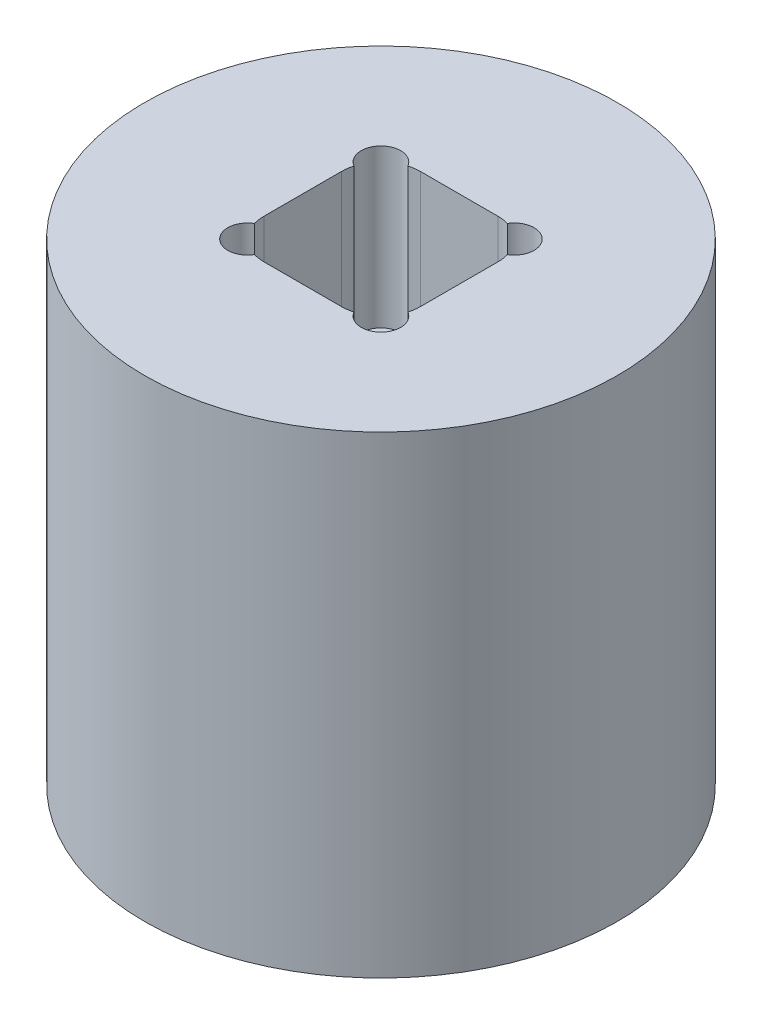
SolidWorks part; units mm, degrees
ref_plane "Front Plane" through (0, 0, 0) normal (0, 0, 1) x (1, 0, 0)
ref_plane "Top Plane" through (0, 0, 0) normal (0, 1, 0) x (1, 0, 0)
ref_plane "Right Plane" through (0, 0, 0) normal (1, 0, 0) x (0, 0, -1)
sketch "Sketch1" plane through (0, 0, 0) normal (0, 1, 0) x (1, 0, 0)
  circle A0 centre (0, 0) radius 19.05
  dimension "D1" = 38.1
extrude "Boss-Extrude1" add sketch "Sketch1" along normal mid plane 38.1
sketch "Sketch2" plane through (0, 19.05, 0) normal (0, 1, 0) x (1, 0, 0)
  line L1 (6.3056, -6.3056) -> (-6.3056, -6.3056)
  line L2 (6.3056, -6.3056) -> (6.3056, 6.3056)
  line L3 (6.3056, 6.3056) -> (-6.3056, 6.3055)
  line L4 (-6.3056, -6.3056) -> (-6.3056, 6.3055)
  line L5 (6.3056, -6.3056) -> (-6.3056, 6.3055) construction
  line L6 (6.3056, 6.3056) -> (-6.3056, -6.3056) construction
  circle A0 centre (-6.3056, 6.3055) radius 1.5875
  circle A1 centre (-6.3056, -6.3056) radius 1.5875
  circle A2 centre (6.3056, -6.3056) radius 1.5875
  circle A3 centre (6.3056, 6.3056) radius 1.5875
  point P0 (0, 0)
  dimension "D2" = 3.175
  dimension "D1" = 12.6111
extrude "Cut-Extrude1" cut sketch "Sketch2" against normal blind 12.7 contours L4 A0 L3 | A3 L3 A0 L4 A1 L1 A2 L2 | L1 A1 L4 | L2 A2 L1 | L3 A3 L2
sketch "Sketch3" plane through (0, -19.05, 0) normal (0, -1, 0) x (1, 0, 0)
  line L1 (9.1249, 12.3) -> (-9.125, 12.3)
  line L2 (12.2999, 9.125) -> (12.2999, -9.1249)
  line L3 (9.1249, -12.3) -> (-9.125, -12.3)
  line L4 (-12.3, 9.125) -> (-12.3, -9.125)
  line L5 (12.2999, 12.3) -> (-12.3, -12.3) construction
  line L6 (12.2999, -12.3) -> (-12.3, 12.2999) construction
  arc A0 (9.1249, 12.3) -> (12.2999, 9.125) centre (9.1249, 9.125) cw
  arc A1 (-9.125, 12.3) -> (-12.3, 9.125) centre (-9.125, 9.125) ccw
  arc A2 (-9.125, -12.3) -> (-12.3, -9.125) centre (-9.125, -9.125) cw
  arc A3 (12.2999, -9.1249) -> (9.1249, -12.3) centre (9.1249, -9.125) cw
  point P0 (0, 0)
  dimension "D2" = 3.175
  dimension "D1" = 24.5999
extrude "Cut-Extrude2" cut sketch "Sketch3" against normal blind 19.05
fillet "Fillet1" radius 3.175 4 edges at (6.3056, 12.7, 6.3056) (-6.3056, 12.7, 6.3056) (-6.3056, 12.7, -6.3055) (6.3056, 12.7, -6.3056)
sketch "Sketch4" plane through (0, 19.05, 0) normal (0, 1, 0) x (1, 0, 0)
  line L0 (3.1305, 6.3055) -> (-3.1306, 6.3055) construction
  line L1 (6.3055, -6.3055) -> (-6.3056, -6.3055)
  line L2 (6.3055, -6.3055) -> (6.3055, 6.3055)
  line L3 (6.3055, 6.3055) -> (-6.3056, 6.3055)
  line L4 (-6.3056, -6.3055) -> (-6.3056, 6.3055)
  line L5 (6.3055, -6.3055) -> (-6.3056, 6.3055) construction
  line L6 (6.3055, 6.3055) -> (-6.3056, -6.3055) construction
  line L7 (-6.3056, -3.1306) -> (-6.3056, 3.1305) construction
  arc A0 (-3.1306, 6.3055) -> (-6.3056, 3.1305) centre (-3.1306, 3.1305) ccw construction
  circle A1 centre (-5.3756, 5.3756) radius 1.5875
  circle A2 centre (5.3756, 5.3756) radius 1.5875
  circle A3 centre (5.3756, -5.3756) radius 1.5875
  arc A4 (3.1306, -6.3056) -> (6.3056, -3.1306) centre (3.1306, -3.1306) ccw construction
  circle A5 centre (-5.3756, -5.3756) radius 1.5875
  arc A6 (-6.3056, -3.1306) -> (-3.1305, -6.3056) centre (-3.1306, -3.1306) ccw construction
  arc A7 (6.3056, 3.1305) -> (3.1305, 6.3055) centre (3.1306, 3.1305) ccw construction
  point P0 (0, 0)
  point P29 (5.3756, 5.3756)
  point P30 (6.9551, 6.9551)
  arc M9 (6.3056, -3.1306) -> (3.1306, -6.3056) centre (3.1306, -3.1306) cw
  arc M11 (-3.1305, -6.3056) -> (-6.3056, -3.1306) centre (-3.1306, -3.1306) cw
  arc M13 (-6.3056, 3.1305) -> (-3.1306, 6.3055) centre (-3.1306, 3.1305) cw
  arc M15 (3.1305, 6.3055) -> (6.3056, 3.1305) centre (3.1306, 3.1305) cw
  dimension "D1" = 3.175
extrude "Cut-Extrude3" cut sketch "Sketch4" against normal blind 12.7 contours A2 M15 | A2 L2 L3 M15 | L2 A2 L3 | A1 M13 | A1 L3 L4 M13 | L3 A1 L4 | L4 A5 L1 | L1 A5 L4 M11 | A5 M11 | A3 M9 | L2 A3 L1 M9 | L1 A3 L2
